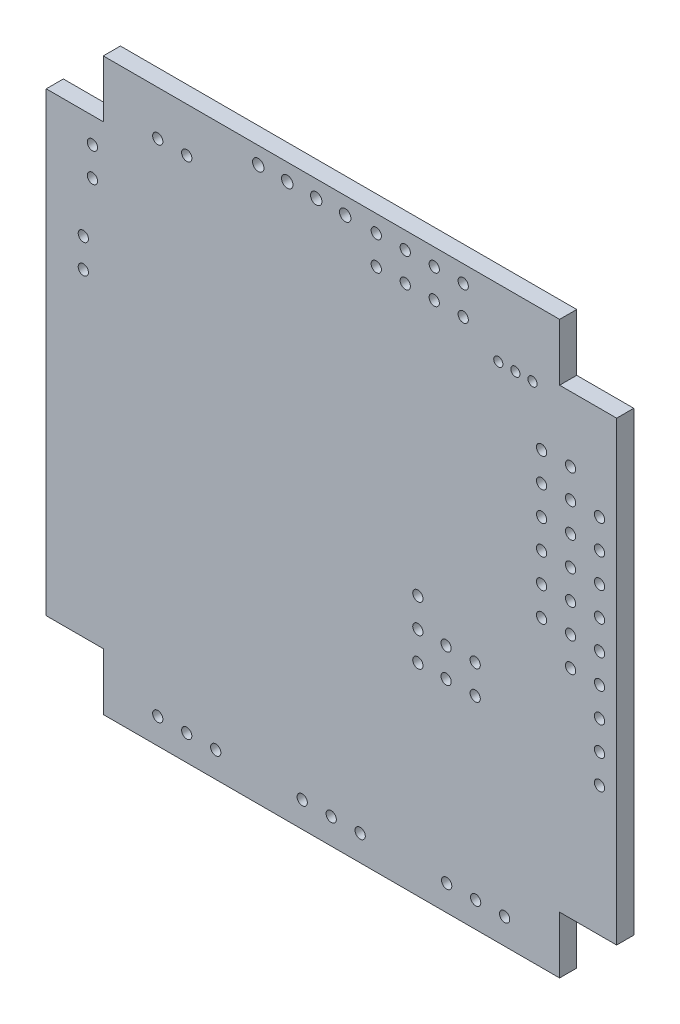
SolidWorks part; units mm, degrees
ref_plane "Спереди" through (0, 0, 0) normal (0, 0, 1) x (1, 0, 0)
ref_plane "Сверху" through (0, 0, 0) normal (0, 1, 0) x (1, 0, 0)
ref_plane "Справа" through (0, 0, 0) normal (1, 0, 0) x (0, 0, -1)
sketch "Эскиз3" plane through (0, 0, 0) normal (0, 0, 1) x (1, 0, 0)
  line L12 (24.0812, -17.7588) -> (24.0812, 22.2412)
  line L13 (19.0812, -17.7588) -> (24.0812, -17.7588)
  line L14 (19.0812, -22.7588) -> (19.0812, -17.7588)
  line L15 (-20.9188, -22.7588) -> (19.0812, -22.7588)
  line L16 (-20.9188, -17.7588) -> (-20.9188, -22.7588)
  line L17 (-25.9188, -17.7588) -> (-20.9188, -17.7588)
  line L18 (-25.9188, 22.2412) -> (-25.9188, -17.7588)
  line L19 (-20.9188, 22.2412) -> (-25.9188, 22.2412)
  line L20 (-20.9188, 27.2412) -> (-20.9188, 22.2412)
  line L21 (19.0812, 27.2412) -> (-20.9188, 27.2412)
  line L22 (19.0812, 22.2412) -> (19.0812, 27.2412)
  line L23 (24.0812, 22.2412) -> (19.0812, 22.2412)
  line L24 (24.0812, -17.7588) -> (24.0812, 22.2412)
  line L25 (19.0812, -17.7588) -> (24.0812, -17.7588)
  line L26 (19.0812, -22.7588) -> (19.0812, -17.7588)
  line L27 (-20.9188, -22.7588) -> (19.0812, -22.7588)
  line L28 (-20.9188, -17.7588) -> (-20.9188, -22.7588)
  line L29 (-25.9188, -17.7588) -> (-20.9188, -17.7588)
  line L30 (-25.9188, 22.2412) -> (-25.9188, -17.7588)
  line L31 (-20.9188, 22.2412) -> (-25.9188, 22.2412)
  line L32 (-20.9188, 27.2412) -> (-20.9188, 22.2412)
  line L33 (19.0812, 27.2412) -> (-20.9188, 27.2412)
  line L34 (19.0812, 22.2412) -> (19.0812, 27.2412)
  line L35 (24.0812, 22.2412) -> (19.0812, 22.2412)
  circle A0 centre (-21.8688, 17.4762) radius 0.45 construction
  circle A1 centre (22.5813, 1.2412) radius 0.45
  circle A2 centre (22.5813, 1.2412) radius 0.45
  circle A3 centre (22.5813, 3.7912) radius 0.45
  circle A4 centre (22.5813, 3.7912) radius 0.45
  circle A5 centre (22.5813, 6.3412) radius 0.45
  circle A6 centre (22.5813, 6.3412) radius 0.45
  circle A7 centre (22.5813, 8.8912) radius 0.45
  circle A8 centre (22.5813, 8.8912) radius 0.45
  circle A9 centre (22.5813, 11.4412) radius 0.45
  circle A10 centre (22.5813, 11.4412) radius 0.45
  circle A11 centre (22.5813, 13.9912) radius 0.45
  circle A12 centre (22.5813, 13.9912) radius 0.45
  circle A13 centre (17.5013, 3.7912) radius 0.45
  circle A14 centre (17.5013, 3.7912) radius 0.45
  circle A15 centre (17.5013, 6.3412) radius 0.45
  circle A16 centre (17.5013, 6.3412) radius 0.45
  circle A17 centre (17.5013, 8.8912) radius 0.45
  circle A18 centre (17.5013, 8.8912) radius 0.45
  circle A19 centre (17.5013, 11.4412) radius 0.45
  circle A20 centre (17.5013, 11.4412) radius 0.45
  circle A21 centre (17.5013, 13.9912) radius 0.45
  circle A22 centre (17.5013, 13.9912) radius 0.45
  circle A23 centre (17.5013, 16.5412) radius 0.45
  circle A24 centre (17.5013, 16.5412) radius 0.45
  circle A25 centre (20.0413, 16.5412) radius 0.45
  circle A26 centre (20.0413, 16.5412) radius 0.45
  circle A27 centre (20.0413, 13.9912) radius 0.45
  circle A28 centre (20.0413, 13.9912) radius 0.45
  circle A29 centre (20.0413, 11.4412) radius 0.45
  circle A30 centre (20.0413, 11.4412) radius 0.45
  circle A31 centre (20.0413, 8.8912) radius 0.45
  circle A32 centre (20.0413, 8.8912) radius 0.45
  circle A33 centre (20.0413, 6.3412) radius 0.45
  circle A34 centre (20.0413, 6.3412) radius 0.45
  circle A35 centre (20.0413, 3.7912) radius 0.45
  circle A36 centre (20.0413, 3.7912) radius 0.45
  circle A37 centre (20.0413, 1.2412) radius 0.45
  circle A38 centre (20.0413, 1.2412) radius 0.45
  circle A39 centre (22.5812, -6.3888) radius 0.45
  circle A40 centre (22.5812, -6.3888) radius 0.45
  circle A41 centre (22.5812, -3.8488) radius 0.45
  circle A42 centre (22.5812, -3.8488) radius 0.45
  circle A43 centre (22.5812, -1.3088) radius 0.45
  circle A44 centre (22.5812, -1.3088) radius 0.45
  circle A45 centre (3.0112, 25.7412) radius 0.45
  circle A46 centre (3.0112, 25.7412) radius 0.45
  circle A47 centre (5.5512, 23.2012) radius 0.45
  circle A48 centre (5.5512, 23.2012) radius 0.45
  circle A49 centre (5.5512, 25.7412) radius 0.45
  circle A50 centre (5.5512, 25.7412) radius 0.45
  circle A51 centre (8.0912, 23.2012) radius 0.45
  circle A52 centre (8.0912, 23.2012) radius 0.45
  circle A53 centre (8.0912, 25.7412) radius 0.45
  circle A54 centre (8.0912, 25.7412) radius 0.45
  circle A55 centre (10.6312, 25.7412) radius 0.45
  circle A56 centre (10.6312, 25.7412) radius 0.45
  circle A57 centre (10.6312, 23.2012) radius 0.45
  circle A58 centre (10.6312, 23.2012) radius 0.45
  circle A59 centre (13.7062, 21.3412) radius 0.4
  circle A60 centre (13.7062, 21.3412) radius 0.4
  circle A61 centre (15.2062, 21.3412) radius 0.4
  circle A62 centre (15.2062, 21.3412) radius 0.4
  circle A63 centre (16.7062, 21.3412) radius 0.4
  circle A64 centre (16.7062, 21.3412) radius 0.4
  circle A65 centre (6.6563, 0.0412) radius 0.45
  circle A66 centre (6.6563, 0.0412) radius 0.45
  circle A67 centre (6.6563, -5.0388) radius 0.45
  circle A68 centre (6.6563, -5.0388) radius 0.45
  circle A69 centre (6.6563, -2.4988) radius 0.45
  circle A70 centre (6.6563, -2.4988) radius 0.45
  circle A71 centre (9.1313, -2.4988) radius 0.45
  circle A72 centre (9.1313, -2.4988) radius 0.45
  circle A73 centre (9.1313, -5.0388) radius 0.45
  circle A74 centre (9.1313, -5.0388) radius 0.45
  circle A75 centre (11.6814, -2.4988) radius 0.45
  circle A76 centre (11.6814, -2.4988) radius 0.45
  circle A77 centre (14.2613, -20.5088) radius 0.45
  circle A78 centre (14.2613, -20.5088) radius 0.45
  circle A79 centre (11.7213, -20.5088) radius 0.45
  circle A80 centre (11.7213, -20.5088) radius 0.45
  circle A81 centre (9.1813, -20.5088) radius 0.45
  circle A82 centre (9.1813, -20.5088) radius 0.45
  circle A83 centre (1.5988, -20.5088) radius 0.45
  circle A84 centre (1.5988, -20.5088) radius 0.45
  circle A85 centre (-0.9412, -20.5088) radius 0.45
  circle A86 centre (-0.9412, -20.5088) radius 0.45
  circle A87 centre (-3.4812, -20.5088) radius 0.45
  circle A88 centre (-3.4812, -20.5088) radius 0.45
  circle A89 centre (-11.0637, -20.5088) radius 0.45
  circle A90 centre (-11.0637, -20.5088) radius 0.45
  circle A91 centre (-13.6037, -20.5088) radius 0.45
  circle A92 centre (-13.6037, -20.5088) radius 0.45
  circle A93 centre (-16.1437, -20.5088) radius 0.45
  circle A94 centre (-16.1437, -20.5088) radius 0.45
  circle A95 centre (-22.6688, 10.1412) radius 0.45
  circle A96 centre (-22.6688, 10.1412) radius 0.45
  circle A97 centre (-22.6688, 12.6812) radius 0.45
  circle A98 centre (-22.6688, 12.6812) radius 0.45
  circle A99 centre (-7.3338, 25.7562) radius 0.5
  circle A100 centre (-7.3338, 25.7562) radius 0.5
  circle A101 centre (-4.7938, 25.7562) radius 0.5
  circle A102 centre (-4.7938, 25.7562) radius 0.5
  circle A103 centre (-2.2538, 25.7562) radius 0.5
  circle A104 centre (-2.2538, 25.7562) radius 0.5
  circle A105 centre (0.2862, 25.7562) radius 0.5
  circle A106 centre (0.2862, 25.7562) radius 0.5
  circle A107 centre (3.0112, 23.2012) radius 0.45
  circle A108 centre (3.0112, 23.2012) radius 0.45
  circle A109 centre (11.6814, -5.0388) radius 0.45
  circle A110 centre (11.6814, -5.0388) radius 0.45
  circle A111 centre (-21.8688, 20.0162) radius 0.45 construction
  circle A112 centre (-16.1438, 23.3412) radius 0.45 construction
  circle A113 centre (-13.6038, 23.3412) radius 0.45 construction
  circle A114 centre (-21.8688, 17.4762) radius 0.45
  circle A115 centre (-21.8688, 20.0162) radius 0.45
  circle A116 centre (-16.1438, 23.3412) radius 0.45
  circle A117 centre (-13.6038, 23.3412) radius 0.45
  dimension "D1" = 0
  dimension "D2" = 0
  dimension "D3" = 0
  dimension "D4" = 0
  dimension "D5" = 0
  dimension "D6" = 0
  dimension "D7" = 0
  dimension "D8" = 0
  dimension "D9" = 0
  dimension "D10" = 0
  dimension "D11" = 0
  dimension "D12" = 0
  dimension "D13" = 0
  dimension "D14" = 0
  dimension "D15" = 0
  dimension "D16" = 0
  dimension "D17" = 0
  dimension "D18" = 0
  dimension "D19" = 0
  dimension "D20" = 0
  dimension "D21" = 0
  dimension "D22" = 0
  dimension "D23" = 0
  dimension "D24" = 0
  dimension "D25" = 0
  dimension "D26" = 0
  dimension "D27" = 0
  dimension "D28" = 0
  dimension "D29" = 0
  dimension "D30" = 0
  dimension "D31" = 0
  dimension "D32" = 0
  dimension "D33" = 0
  dimension "D34" = 0
  dimension "D35" = 0
  dimension "D36" = 0
  dimension "D37" = 0
  dimension "D38" = 0
  dimension "D39" = 0
  dimension "D40" = 0
  dimension "D41" = 0
  dimension "D42" = 0
  dimension "D43" = 0
  dimension "D44" = 0
  dimension "D45" = 0
  dimension "D46" = 0
  dimension "D47" = 0
  dimension "D48" = 0
  dimension "D49" = 0
  dimension "D50" = 0
  dimension "D51" = 0
  dimension "D52" = 0
  dimension "D53" = 0
  dimension "D54" = 0
  dimension "D55" = 0
  dimension "D56" = 0
extrude "Бобышка-Вытянуть1" add sketch "Эскиз3" along normal blind 1.5
sketch "Эскиз4" plane through (0, 0, 1.5) normal (0, 0, 1) x (1, 0, 0)
  line L0 (-20.9188, -22.7588) -> (19.0812, -22.7588) construction
  line L1 (-25.9188, 22.2412) -> (-25.9188, -17.7588) construction
  point P0 (-25.9188, -22.7588)
